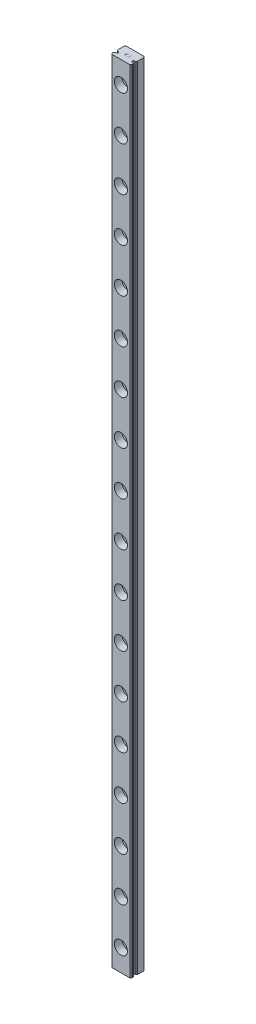
SolidWorks part; units mm, degrees
material "acero"
ref_plane "Alzado" through (0, 0, 0) normal (0, 0, 1) x (1, 0, 0)
ref_plane "Planta" through (0, 0, 0) normal (0, 1, 0) x (1, 0, 0)
ref_plane "Vista lateral" through (0, 0, 0) normal (1, 0, 0) x (0, 0, -1)
ref_plane "Plano1" through (0, 0, 0) normal (0, -1, 0) x (1, 0, 0)
sketch "Croquis1" plane through (0, 0, 0) normal (0, -1, 0) x (1, 0, 0)
  line L0 (4.5, 0) -> (4.5, 6.0117)
  line L1 (4.5, 6.0117) -> (4.1, 6.5)
  line L2 (4.1, 6.5) -> (-4.1, 6.5)
  line L3 (-4.1, 6.5) -> (-4.5, 6.0117)
  line L4 (-4.5, 6.0117) -> (-4.5, 0)
  line L5 (-4.5, 0) -> (4.5, 0)
extrude "Saliente-Extruir1" add sketch "Croquis1" against normal blind 360
sketch "Croquis2" plane through (0, 360, 0) normal (0, 1, 0) x (-1, 0, 0)
  line L0 (-4.5, 4.8802) -> (-4.5, 4.0315)
  line L1 (-4.5, 4.0315) -> (-3.8193, 4.0315)
  line L2 (-3.8193, 4.8802) -> (-4.5, 4.8802)
  arc A1 (-3.8193, 4.0315) -> (-3.8193, 4.8802) centre (-3.6695, 4.4558) ccw
  dimension "D4" = 0.9
  dimension "D2" = 0.8487
extrude "Cortar-Extruir1" cut sketch "Croquis2" against normal through all
sketch "Croquis3" plane through (0, 360, 0) normal (0, 1, 0) x (-1, 0, 0)
  line L0 (-4.0265, 4.0315) -> (-4.5, 4.0315)
  line L1 (-4.5, 4.0315) -> (-4.5, 3.5836)
  arc A0 (-4.5, 3.5836) -> (-4.0265, 4.0315) centre (-4.8765, 4.4558) ccw
extrude "Cortar-Extruir2" cut sketch "Croquis3" against normal through all
sketch "Croquis4" plane through (0, 360, 0) normal (0, 1, 0) x (-1, 0, 0)
  line L0 (-4.5, 5.3281) -> (-4.5, 4.8802)
  line L1 (-4.5, 4.8802) -> (-4.0265, 4.8802)
  arc A0 (-4.0265, 4.8802) -> (-4.5, 5.3281) centre (-4.8765, 4.4558) ccw
extrude "Cortar-Extruir3" cut sketch "Croquis4" against normal through all
sketch "Croquis5" plane through (0, 360, 0) normal (0, 1, 0) x (-1, 0, 0)
  line L0 (4.5, 4.0315) -> (4.5, 4.8802)
  line L1 (4.5, 4.8802) -> (3.8193, 4.8802)
  line L2 (3.8193, 4.0315) -> (4.5, 4.0315)
  arc A1 (3.8193, 4.8802) -> (3.8193, 4.0315) centre (3.6695, 4.4558) ccw
  dimension "D3" = 0.9
  dimension "D2" = 0.8487
extrude "Cortar-Extruir4" cut sketch "Croquis5" against normal through all
sketch "Croquis6" plane through (0, 360, 0) normal (0, 1, 0) x (-1, 0, 0)
  line L0 (4.0265, 4.8802) -> (4.5, 4.8802)
  line L1 (4.5, 4.8802) -> (4.5, 5.3281)
  arc A0 (4.5, 5.3281) -> (4.0265, 4.8802) centre (4.8765, 4.4558) ccw
extrude "Cortar-Extruir5" cut sketch "Croquis6" against normal through all
sketch "Croquis7" plane through (0, 360, 0) normal (0, 1, 0) x (-1, 0, 0)
  line L0 (4.5, 3.5836) -> (4.5, 4.0315)
  line L1 (4.5, 4.0315) -> (4.0265, 4.0315)
  arc A0 (4.0265, 4.0315) -> (4.5, 3.5836) centre (4.8765, 4.4558) ccw
extrude "Cortar-Extruir6" cut sketch "Croquis7" against normal through all
sketch "Croquis8" plane through (0, 360, 0) normal (0, 1, 0) x (-1, 0, 0)
  line L0 (0.8914, 3.4037) -> (0.7147, 3.1682)
  line L1 (0.7147, 3.1682) -> (0.2187, 2.611)
  line L2 (0.2187, 2.611) -> (1.0946, 2.6111)
  line L3 (1.0946, 2.6111) -> (1.0946, 2.696)
  line L4 (1.0946, 2.696) -> (0.3987, 2.696)
  line L5 (0.3987, 2.696) -> (0.7943, 3.1495)
  line L6 (0.7943, 3.1495) -> (0.9743, 3.3891)
  line L7 (0.9743, 3.3891) -> (1.0671, 3.5734)
  line L8 (1.0671, 3.5734) -> (0.9541, 3.8023)
  line L9 (0.9541, 3.8023) -> (0.7877, 3.8851)
  line L10 (0.7877, 3.8851) -> (0.543, 3.8851)
  line L11 (0.543, 3.8851) -> (0.3754, 3.8036)
  line L12 (0.3754, 3.8036) -> (0.295, 3.6384)
  line L13 (0.295, 3.6384) -> (0.295, 3.562)
  line L14 (0.295, 3.562) -> (0.3813, 3.562)
  line L15 (0.3813, 3.562) -> (0.3813, 3.6318)
  line L16 (0.3813, 3.6318) -> (0.4377, 3.7436)
  line L17 (0.4377, 3.7436) -> (0.5496, 3.8001)
  line L18 (0.5496, 3.8001) -> (0.7802, 3.8001)
  line L19 (0.7802, 3.8001) -> (0.893, 3.7438)
  line L20 (0.893, 3.7438) -> (0.9762, 3.576)
  line L21 (0.9762, 3.576) -> (0.8914, 3.4037)
extrude "Cortar-Extruir7" cut sketch "Croquis8" against normal blind 0.0022
sketch "Croquis9" plane through (0, 0, 0) normal (0, -1, 0) x (1, 0, 0)
  line L0 (-0.2146, 3.8851) -> (-0.954, 3.8851)
  line L1 (-0.954, 3.8851) -> (-0.954, 2.6111)
  line L2 (-0.954, 2.6111) -> (-0.2146, 2.6111)
  line L3 (-0.2146, 2.6111) -> (-0.2146, 2.696)
  line L4 (-0.2146, 2.696) -> (-0.869, 2.696)
  line L5 (-0.869, 2.696) -> (-0.869, 3.2056)
  line L6 (-0.869, 3.2056) -> (-0.5124, 3.2056)
  line L7 (-0.5124, 3.2056) -> (-0.5124, 3.2905)
  line L8 (-0.5124, 3.2905) -> (-0.869, 3.2905)
  line L9 (-0.869, 3.2905) -> (-0.869, 3.8001)
  line L10 (-0.869, 3.8001) -> (-0.2146, 3.8001)
  line L11 (-0.2146, 3.8001) -> (-0.2146, 3.8851)
extrude "Cortar-Extruir8" cut sketch "Croquis9" against normal blind 0.0022
sketch "Croquis10" plane through (0, 360, 0) normal (0, 1, 0) x (-1, 0, 0)
  line L0 (-0.2146, 3.8851) -> (-0.954, 3.8851)
  line L1 (-0.954, 3.8851) -> (-0.954, 2.6111)
  line L2 (-0.954, 2.6111) -> (-0.2146, 2.6111)
  line L3 (-0.2146, 2.6111) -> (-0.2146, 2.696)
  line L4 (-0.2146, 2.696) -> (-0.869, 2.696)
  line L5 (-0.869, 2.696) -> (-0.869, 3.2056)
  line L6 (-0.869, 3.2056) -> (-0.5124, 3.2056)
  line L7 (-0.5124, 3.2056) -> (-0.5124, 3.2905)
  line L8 (-0.5124, 3.2905) -> (-0.869, 3.2905)
  line L9 (-0.869, 3.2905) -> (-0.869, 3.8001)
  line L10 (-0.869, 3.8001) -> (-0.2146, 3.8001)
  line L11 (-0.2146, 3.8001) -> (-0.2146, 3.8851)
extrude "Cortar-Extruir9" cut sketch "Croquis10" against normal blind 0.0022
sketch "Croquis11" plane through (0, 0, 0) normal (0, -1, 0) x (1, 0, 0)
  line L0 (0.5101, 3.6208) -> (0.6071, 3.7187)
  line L1 (0.6071, 3.7187) -> (0.6071, 2.6094)
  line L2 (0.6071, 2.6094) -> (0.692, 2.6094)
  line L3 (0.692, 2.6094) -> (0.692, 3.8834)
  line L4 (0.692, 3.8834) -> (0.6741, 3.8834)
  line L5 (0.6741, 3.8834) -> (0.6741, 3.7951)
  line L6 (0.6741, 3.7951) -> (0.3691, 3.6407)
  line L7 (0.3691, 3.6407) -> (0.3691, 3.5513)
  line L8 (0.3691, 3.5513) -> (0.5101, 3.6208)
extrude "Cortar-Extruir10" cut sketch "Croquis11" against normal blind 0.0022
draft "Ángulo de salida1" type of draft neutral plane draft angle 45.147 faces to draft 1 face at (0.6741, 0.0011, 3.8392) neutral plane through (0.692, 0.0022, 3.8834) neutral plane normal (0, 0, -1) parameters "D1"=45.147
hole_wizard "Taladro roscado M3.5x0.61" positions "Croquis35" profile "Croquis34" tap size "M3.5x0.6" standard "Ansi Metric"
sketch "Croquis35" plane through (0, 0, 0) normal (0, 0, -1) x (-1, 0, 0)
  line L0 (-4.1, 360) -> (4.1, 360) construction
  line L3 (0, 0) -> (0, 360) construction
  line L4 (4.5, 0) -> (-4.5, 0) construction
  point P1 (0, 330)
  point P2 (0, 310)
  point P3 (0, 290)
  point P4 (0, 270)
  point P5 (0, 250)
  point P6 (0, 230)
  point P7 (0, 210)
  point P8 (0, 190)
  point P9 (0, 170)
  point P10 (0, 150)
  point P11 (0, 130)
  point P12 (0, 110)
  point P13 (0, 90)
  point P14 (0, 70)
  point P15 (0, 50)
  point P16 (0, 30)
  point P39 (0, 10)
  point P45 (0, 350)
  dimension "D1" = 20
  dimension "D3" = 20
  dimension "D4" = 20
  dimension "D5" = 20
  dimension "D6" = 20
  dimension "D7" = 20
  dimension "D8" = 20
  dimension "D9" = 20
  dimension "D10" = 20
  dimension "D11" = 20
  dimension "D12" = 20
  dimension "D13" = 20
  dimension "D14" = 20
  dimension "D15" = 20
  dimension "D16" = 20
  dimension "D17" = 20
  dimension "D18" = 20
  dimension "D20" = 10
sketch "Croquis34" plane through (0, 330, 0) normal (1, 0, 0) x (0, 1, 0)
  line L0 (0, 0) -> (0, 6.09)
  line L1 (0, 6.09) -> (3, 6.09)
  line L2 (3, 6.09) -> (3, 3)
  line L3 (3, 3) -> (1.75, 3)
  line L4 (1.75, 3) -> (1.75, 0)
  line L5 (1.75, 0) -> (0, 0)
  line L10 (0, 6.09) -> (-3, 6.09) construction
  line L11 (0, -6.35) -> (0, 107.95) construction
  dimension "Diámetro de perforador para roscar" = 6
  dimension "Profundidad de perforador para roscar" = 6.09
  dimension "Diámetro mayor de rosca" = 3.5
  dimension "Profundidad de rosca" = 3
  dimension "Ángulo de perforador" = 180
chamfer "Chaflán1" distance 0.4 angle 45 2 edges at (4.5, 180, 0) (-4.5, 180, 0)
fillet "Redondeo1" radius 0.13 8 edges at (4.5, 180, 3.5836) (4.0265, 180, 4.0315) (-4.0265, 180, 4.0315) (-4.0265, 180, 4.8802) (-4.5, 180, 5.3281) (-4.5, 180, 3.5836) (4.5, 180, 5.3281) (4.0265, 180, 4.8802)
sketch "Sketch1" plane through (0, 0, 6.5) normal (0, 0, 1) x (1, 0, 0)
  line L0 (4.1, 0) -> (-4.1, 0) construction
  line L1 (4.1, 360) -> (4.1, 0) construction
  circle A0 centre (0, 10) radius 3
  circle A1 centre (0, 30) radius 3
  circle A2 centre (0, 50) radius 3
  circle A3 centre (0, 70) radius 3
  circle A4 centre (0, 90) radius 3
  circle A5 centre (0, 110) radius 3
  circle A6 centre (0, 130) radius 3
  circle A7 centre (0, 150) radius 3
  circle A8 centre (0, 170) radius 3
  circle A9 centre (0, 190) radius 3
  circle A10 centre (0, 210) radius 3
  circle A11 centre (0, 230) radius 3
  circle A12 centre (0, 250) radius 3
  circle A13 centre (0, 270) radius 3
  circle A14 centre (0, 290) radius 3
  circle A15 centre (0, 310) radius 3
  circle A16 centre (0, 330) radius 3
  circle A17 centre (0, 350) radius 3
  point P0 (0, 390)
  point P1 (0, 370)
  point P2 (0, 350)
  point P3 (0, 330)
  point P4 (0, 310)
  point P5 (0, 290)
  point P6 (0, 270)
  point P7 (0, 250)
  point P8 (0, 230)
  point P9 (0, 210)
  point P10 (0, 190)
  point P11 (0, 170)
  point P12 (0, 150)
  point P13 (0, 130)
  point P14 (0, 110)
  point P15 (0, 90)
  point P16 (0, 70)
  point P17 (0, 50)
  point P18 (0, 30)
  point P19 (0, 10)
  point P26 (0, 310)
  point P28 (0, 30)
  point P31 (0, 50)
  point P34 (0, 70)
  point P37 (0, 90)
  point P40 (0, 110)
  point P43 (0, 130)
  point P46 (0, 150)
  point P49 (0, 170)
  point P52 (0, 190)
  point P55 (0, 210)
  point P58 (0, 230)
  point P61 (0, 250)
  point P64 (0, 270)
  point P67 (0, 290)
  point P71 (0, 330)
  point P74 (0, 350)
  dimension "D1" = 6
  dimension "D2" = 10
  dimension "D3" = 4.1
  dimension "D4" = 18
extrude "Cut-Extrude1" cut sketch "Sketch1" against normal blind 3
